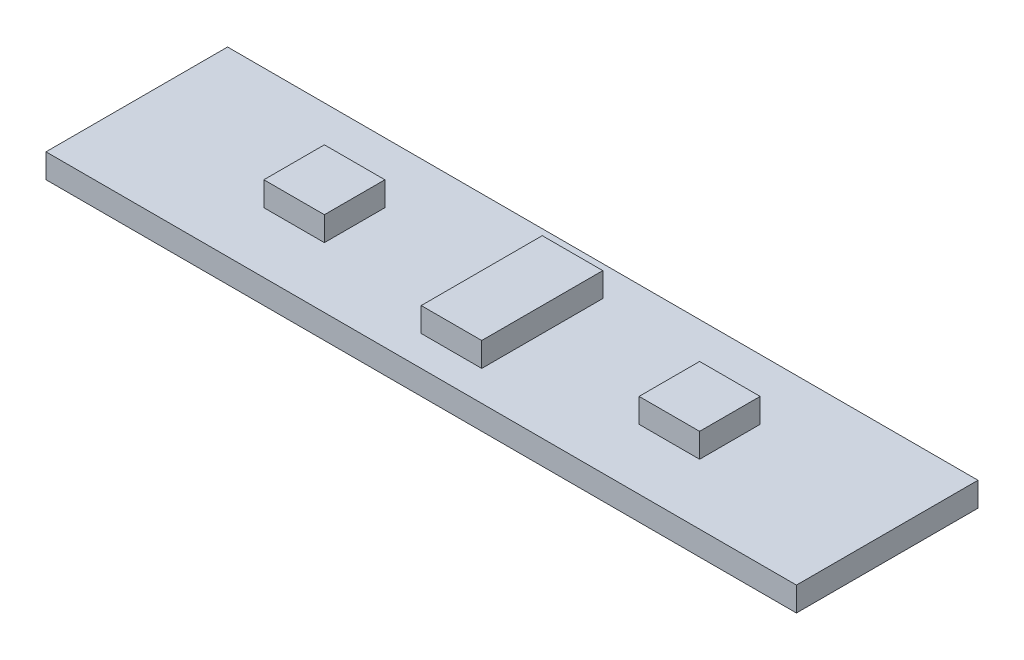
SolidWorks part; units mm, degrees
ref_plane "Front Plane" through (0, 0, 0) normal (0, 0, 1) x (1, 0, 0)
ref_plane "Top Plane" through (0, 0, 0) normal (0, 1, 0) x (1, 0, 0)
ref_plane "Right Plane" through (0, 0, 0) normal (1, 0, 0) x (0, 0, -1)
sketch "Sketch1" plane through (0, 0, 0) normal (0, 1, 0) x (1, 0, 0)
  line L1 (0, 0) -> (62, 0)
  line L2 (0, 0) -> (0, 15)
  line L3 (0, 15) -> (62, 15)
  line L4 (62, 0) -> (62, 15)
  dimension "D1" = 62
  dimension "D2" = 15
extrude "Boss-Extrude1" add sketch "Sketch1" along normal blind 2
sketch "Sketch2" plane through (0, 2, 0) normal (0, 1, 0) x (1, 0, 0)
  line L0 (31, 0) -> (31, 15) construction
  line L1 (13, 10) -> (18, 10)
  line L2 (13, 10) -> (13, 5)
  line L3 (13, 5) -> (18, 5)
  line L4 (18, 10) -> (18, 5)
  line L5 (0, 0) -> (62, 0) construction
  line L6 (62, 15) -> (0, 15) construction
  line L7 (15.5, 5) -> (15.5, 0) construction
  line L8 (15.5, 10) -> (15.5, 15) construction
  line L9 (49, 5) -> (44, 5)
  line L10 (44, 10) -> (44, 5)
  line L11 (49, 10) -> (44, 10)
  line L12 (49, 10) -> (49, 5)
  line L13 (31, 2.5) -> (28.5, 2.5)
  line L14 (28.5, 2.5) -> (28.5, 12.5)
  line L15 (28.5, 12.5) -> (33.5, 12.5)
  line L16 (33.5, 12.5) -> (33.5, 2.5)
  line L17 (33.5, 2.5) -> (31, 2.5)
  dimension "D1" = 5
  dimension "D2" = 13
  dimension "D3" = 5
  dimension "D4" = 10
  dimension "D5" = 2.5
extrude "Boss-Extrude2" add sketch "Sketch2" along normal blind 2
